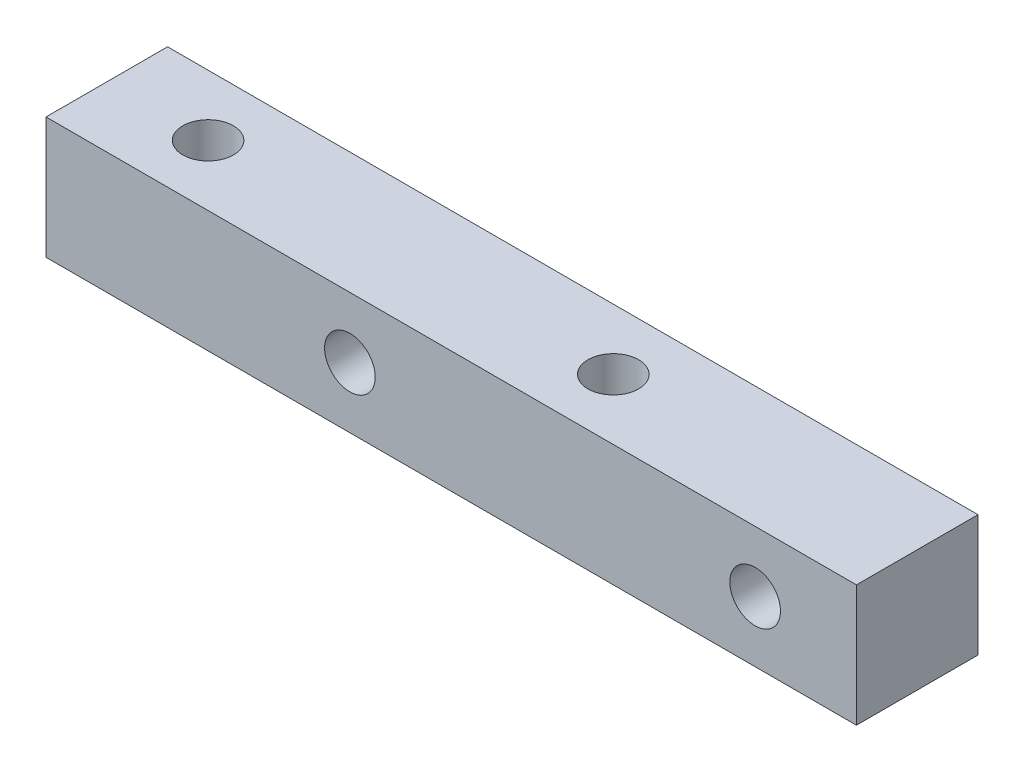
SolidWorks part; units mm, degrees
material "6061 Alloy"
ref_plane "Front Plane" through (0, 0, 0) normal (0, 0, 1) x (1, 0, 0)
ref_plane "Top Plane" through (0, 0, 0) normal (0, 1, 0) x (1, 0, 0)
ref_plane "Right Plane" through (0, 0, 0) normal (1, 0, 0) x (0, 0, -1)
sketch "Sketch1" plane through (0, 0, 0) normal (0, 1, 0) x (1, 0, 0)
  line L1 (-5, -3) -> (35, -3)
  line L2 (-5, -3) -> (-5, 3)
  line L3 (-5, 3) -> (35, 3)
  line L4 (35, -3) -> (35, 3)
  line L5 (-5, -3) -> (35, 3) construction
  line L6 (-5, 3) -> (35, -3) construction
  circle A0 centre (0, 0) radius 1.25
  circle A1 centre (20, 0) radius 1.25
  point P5 (0, 0)
  point P6 (15, 0)
  dimension "D1" = 2.5
  dimension "D2" = 20
  dimension "D5" = 15
  dimension "D3" = 6
  dimension "D4" = 5
extrude "Boss-Extrude1" add sketch "Sketch1" along normal blind 6
sketch "Sketch2" plane through (0, 0, 3) normal (0, 0, 1) x (1, 0, 0)
  line L0 (35, 6) -> (35, 0) construction
  line L1 (-5, 6) -> (35, 6) construction
  circle A0 centre (10, 3) radius 1.25
  circle A1 centre (30, 3) radius 1.25
  point P8 (8.1052, 3)
  dimension "D1" = 2.5
  dimension "D2" = 5
  dimension "D3" = 3
  dimension "D4" = 20
extrude "Cut-Extrude1" cut sketch "Sketch2" against normal blind 6
